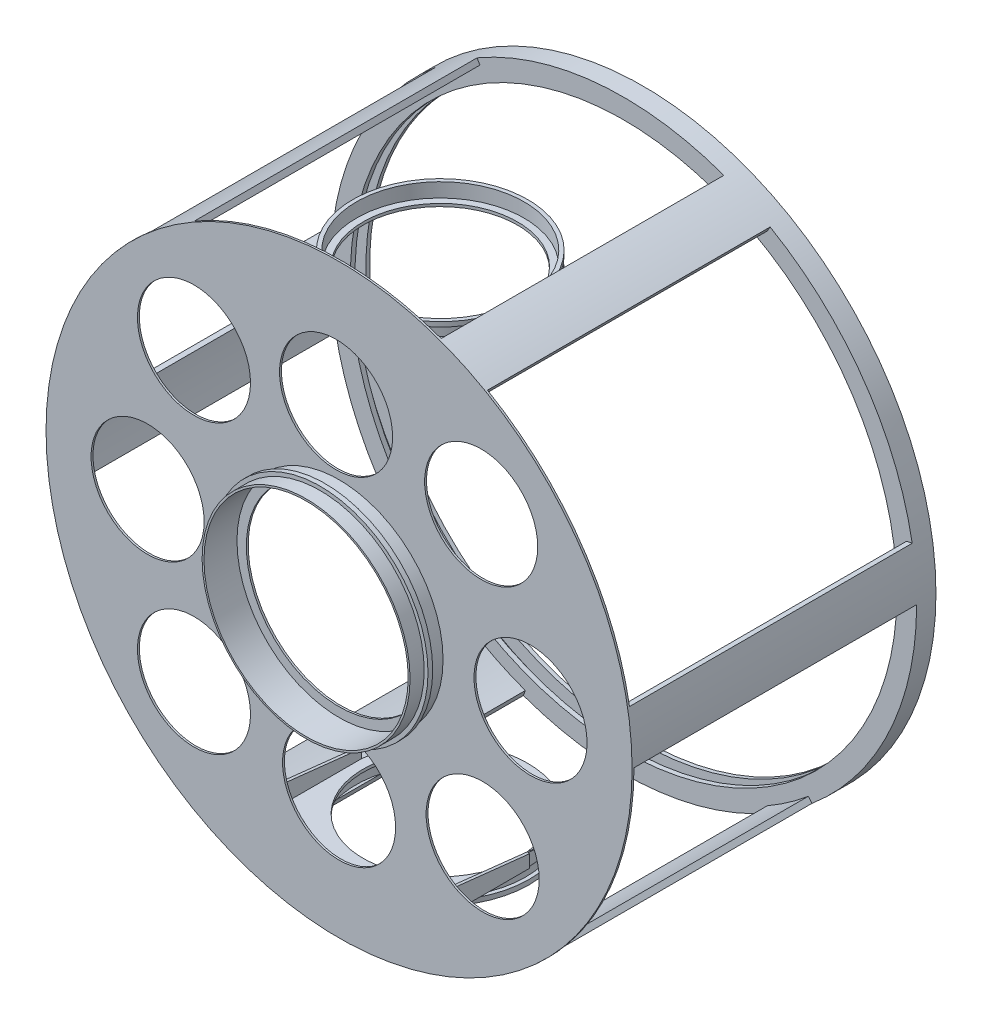
SolidWorks part; units mm, degrees
material "6063-T4"
ref_plane "Front Plane" through (0, 0, 0) normal (0, 0, 1) x (1, 0, 0)
ref_plane "Top Plane" through (0, 0, 0) normal (0, 1, 0) x (1, 0, 0)
ref_plane "Right Plane" through (0, 0, 0) normal (1, 0, 0) x (0, 0, -1)
sketch "Sketch1" plane through (0, 0, 0) normal (0, 0, 1) x (1, 0, 0)
  circle A0 centre (0, 0) radius 290.1
  circle A1 centre (0, 0) radius 311
extrude "Extrude1" add sketch "Sketch1" along normal blind 4
sketch "Sketch3" plane through (0, 0, 4) normal (0, 0, 1) x (1, 0, 0)
  circle A0 centre (0, 0) radius 311
  circle A1 centre (0, 0) radius 305
extrude "Extrude2" add sketch "Sketch3" along normal blind 11.5
sketch "Sketch4" plane through (0, 0, 15.5) normal (0, 0, 1) x (1, 0, 0)
  circle A0 centre (0, 0) radius 311
  circle A1 centre (0, 0) radius 290.1
extrude "Extrude3" add sketch "Sketch4" along normal blind 5
sketch "Sketch5" plane through (0, 0, 20.5) normal (0, 0, 1) x (1, 0, 0)
  line L0 (0, 0) -> (190.5, 0) construction
  line L1 (0, 0) -> (106.0987, 183.7684) construction
  line L2 (0, 0) -> (-108.3258, 187.6258) construction
  line L3 (0, 0) -> (-211.1375, 0) construction
  line L4 (0, 0) -> (-109.7214, -190.043) construction
  line L5 (0, 0) -> (117.9514, -204.2977) construction
  line L6 (0, 0) -> (268.0733, 47.2686) construction
  line L7 (0, 0) -> (77.8476, 213.8846) construction
  line L8 (0, 0) -> (-153.0298, 182.3738) construction
  line L9 (0, 0) -> (-259.4461, -45.7473) construction
  line L10 (0, 0) -> (-74.3455, -204.2625) construction
  line L11 (0, 0) -> (154.9569, -184.6704) construction
  line L12 (300.3664, 52.9627) -> (306.2752, 54.0046)
  line L13 (305, 0) -> (311, 0)
  line L14 (152.5, 264.1377) -> (155.5, 269.3339)
  line L15 (104.3161, 286.6062) -> (106.3683, 292.2444)
  line L16 (-152.5, 264.1377) -> (-155.5, 269.3339)
  line L17 (-196.0502, 233.6436) -> (-199.9069, 238.2398)
  line L18 (-305, 0) -> (-311, 0)
  line L19 (-300.3664, -52.9627) -> (-306.2752, -54.0046)
  line L20 (-152.5, -264.1377) -> (-155.5, -269.3339)
  line L21 (-104.3161, -286.6062) -> (-106.3683, -292.2444)
  line L22 (152.5, -264.1377) -> (155.5, -269.3339)
  line L23 (196.0502, -233.6436) -> (199.9069, -238.2398)
  circle A0 centre (0, 0) radius 311 construction
  circle A1 centre (0, 0) radius 305 construction
  arc A2 (300.3664, 52.9627) -> (305, 0) centre (0, 0) cw
  arc A3 (104.3161, 286.6062) -> (152.5, 264.1377) centre (0, 0) cw
  arc A4 (155.5, 269.3339) -> (106.3683, 292.2444) centre (0, 0) ccw
  arc A6 (-152.5, 264.1377) -> (-196.0502, 233.6436) centre (0, 0) ccw
  arc A7 (-155.5, 269.3339) -> (-199.9069, 238.2398) centre (0, 0) ccw
  arc A8 (-305, 0) -> (-300.3664, -52.9627) centre (0, 0) ccw
  arc A9 (-311, 0) -> (-306.2752, -54.0046) centre (0, 0) ccw
  arc A10 (-152.5, -264.1377) -> (-104.3161, -286.6062) centre (0, 0) ccw
  arc A11 (-155.5, -269.3339) -> (-106.3683, -292.2444) centre (0, 0) ccw
  arc A12 (152.5, -264.1377) -> (196.0502, -233.6436) centre (0, 0) ccw
  arc A13 (155.5, -269.3339) -> (199.9069, -238.2398) centre (0, 0) ccw
  arc A14 (311, 0) -> (306.2752, 54.0046) centre (0, 0) ccw
extrude "Extrude4" add sketch "Sketch5" along normal blind 300
sketch "Sketch6" plane through (0, 0, 320.5) normal (0, 0, 1) x (1, 0, 0)
  circle A0 centre (0, 0) radius 311
extrude "Extrude5" add sketch "Sketch6" along normal blind 2
sketch "Sketch7" plane through (0, 0, 322.5) normal (0, 0, 1) x (1, 0, 0)
  circle A0 centre (0, 0) radius 110.37
  circle A1 centre (0, 0) radius 108.37
extrude "Extrude6" add sketch "Sketch7" along normal blind 15
sketch "Sketch8" plane through (0, 0, 337.5) normal (0, 0, 1) x (1, 0, 0)
  circle A0 centre (0, 0) radius 108.37
  circle A1 centre (0, 0) radius 114.4
extrude "Extrude7" add sketch "Sketch8" along normal blind 5
sketch "Sketch9" plane through (0, 0, 342.5) normal (0, 0, 1) x (1, 0, 0)
  circle A0 centre (0, 0) radius 108.37
  circle A1 centre (0, 0) radius 110.37
extrude "Extrude8" add sketch "Sketch9" along normal blind 15
sketch "Sketch10" plane through (0, 0, 320.5) normal (0, 0, -1) x (-1, 0, 0)
  line L0 (0, 0) -> (0, 334.2218) construction
  line L1 (0, 0) -> (0, -343.8771) construction
  line L2 (0, 250) -> (502.8181, 250) construction
  line L3 (0, 250) -> (-514.35, 250) construction
  line L4 (0, -250) -> (542.182, -250) construction
  line L5 (0, -250) -> (-551.8374, -250) construction
  line L6 (0, 253) -> (404.821, 253) construction
  line L7 (0, 253) -> (-322.9253, 253) construction
  line L8 (0, -253) -> (377.1337, -253) construction
  line L9 (0, -253) -> (-458.931, -253) construction
  line L10 (94.96, 250) -> (94.96, 228)
  line L11 (94.96, 250) -> (94.96, 253)
  line L12 (94.96, 253) -> (0, 253)
  line L13 (0, 253) -> (-94.96, 253)
  line L14 (-94.96, 253) -> (-94.96, 250)
  line L15 (94.96, -250) -> (94.96, -228)
  line L16 (94.96, -250) -> (94.96, -253)
  line L17 (94.96, -253) -> (-94.96, -253)
  line L18 (-94.96, -253) -> (-94.96, -250)
  line L19 (94.96, 253) -> (94.96, 166.3555) construction
  line L20 (-94.96, 253) -> (-94.96, 171.8799) construction
  line L21 (94.96, -253) -> (94.96, -186.8569) construction
  line L22 (-94.96, -253) -> (-94.96, -186.8569) construction
  line L23 (94.96, -228) -> (-94.96, -228) construction
  line L24 (94.96, 228) -> (-94.96, 228) construction
  line L25 (94.96, 228) -> (91.96, 228)
  line L26 (91.96, 228) -> (91.96, 250)
  line L27 (91.96, 250) -> (-91.96, 250)
  line L28 (-91.96, 250) -> (-91.96, 228)
  line L29 (-91.96, 228) -> (-94.96, 228)
  line L30 (-94.96, 228) -> (-94.96, 250)
  line L31 (94.96, -228) -> (91.96, -228)
  line L32 (91.96, -228) -> (91.96, -250)
  line L33 (91.96, -250) -> (-91.96, -250)
  line L34 (-91.96, -250) -> (-91.96, -228)
  line L35 (-91.96, -228) -> (-94.96, -228)
  line L36 (-94.96, -228) -> (-94.96, -250)
  point P3 (0, 250)
  point P5 (0, -250)
  point P11 (0, 253)
  point P13 (0, -253)
  point P19 (94.96, 250)
  point P21 (-94.96, 250)
  point P22 (94.96, -250)
  point P23 (-94.96, -250)
  point P30 (94.96, 228)
  point P35 (-94.96, 228)
  point P36 (94.96, -228)
  point P38 (-94.96, -228)
  point P42 (91.96, -228)
  point P45 (-91.96, 228)
  point P46 (91.96, 228)
  point P47 (-91.96, -228)
  dimension "D1" = 250
  dimension "FROM_C" = 250
  dimension "D2" = 3
  dimension "D3" = 3
  dimension "D4" = 94.96
  dimension "RAD" = 94.96
  dimension "D5" = 94.96
  dimension "D6" = 94.96
  dimension "D7" = 25
  dimension "STRONG" = 25
  dimension "D8" = 25
  dimension "D9" = 25
  dimension "D10" = 3
  dimension "D11" = 3
  dimension "D12" = 3
extrude "Extrude9" add sketch "Sketch10" along normal blind 200
sketch "Sketch11" plane through (0, 253, 0) normal (0, 1, 0) x (1, 0, 0)
  line L0 (-94.96, -120.5) -> (94.96, -120.5) construction
  line L1 (0.3935, -99.9484) -> (0.3935, -349.6766) construction
  circle A0 centre (0.3935, -215.46) radius 90.96
  circle A1 centre (0.3935, -215.46) radius 88.96
  point P0 (0, -120.5)
  point P5 (0.3935, -215.46)
  dimension "D1" = 94.96
extrude "Extrude10" add sketch "Sketch11" along normal blind 10
sketch "Sketch13" plane through (0, 263, 0) normal (0, 1, 0) x (1, 0, 0)
  circle A0 centre (0.3935, -215.46) radius 88.96
  circle A1 centre (0.3935, -215.46) radius 92.96
extrude "Extrude11" add sketch "Sketch13" along normal blind 5
sketch "Sketch14" plane through (0, -253, 0) normal (0, -1, 0) x (1, 0, 0)
  line L0 (94.96, 120.5) -> (-94.96, 120.5) construction
  line L1 (0, 120.5) -> (0, 386.5869) construction
  circle A0 centre (0, 215.46) radius 88.96
  circle A1 centre (0, 215.46) radius 90.96
  point P0 (0, 120.5)
  point P5 (0, 215.46)
  dimension "D1" = 94.96
extrude "Extrude12" add sketch "Sketch14" along normal blind 10
sketch "Sketch15" plane through (0, -263, 0) normal (0, -1, 0) x (1, 0, 0)
  circle A0 centre (0, 215.46) radius 88.96
  circle A1 centre (0, 215.46) radius 94.96
extrude "Extrude13" add sketch "Sketch15" along normal blind 5
sketch "Sketch16" plane through (91.96, 0, 0) normal (-1, 0, 0) x (0, 0, 1)
  line L0 (120.5, 228) -> (320.5, 228) construction
  line L1 (120.5, 228) -> (320.5, 228)
  line L2 (320.5, 228) -> (120.5, 250)
  line L3 (120.5, 228) -> (120.5, 250)
  point P0 (220.5, 228)
  point P1 (120.5, 250)
  point P4 (120.5, 228)
  point P9 (320.5, 228)
extrude "Extrude14" cut sketch "Sketch16" against normal up to surface and the other way up to surface up to face at (94.96, 240.5, 220.5) other way up to face at (-94.96, 240.5, 220.5)
sketch "Sketch17" plane through (-91.96, 0, 0) normal (1, 0, 0) x (0, 0, -1)
  line L0 (-120.5, -228) -> (-320.5, -228) construction
  line L1 (-320.5, -228) -> (-120.5, -228)
  line L2 (-120.5, -228) -> (-120.5, -250)
  line L3 (-120.5, -250) -> (-320.5, -228)
  point P0 (-120.5, -250)
  point P1 (-220.5, -228)
  point P3 (-120.5, -228)
  point P6 (-320.5, -228)
extrude "Extrude15" cut sketch "Sketch17" against normal up to surface and the other way up to surface up to face at (-94.96, -240.5, 220.5) other way up to face at (94.96, -240.5, 220.5)
sketch "Sketch18" plane through (0, 253, 0) normal (0, 1, 0) x (1, 0, 0)
  line L1 (93.1735, -215.46) -> (94.96, -215.46)
  line L2 (94.96, -120.5) -> (94.96, -320.5) construction
  line L3 (94.96, -215.46) -> (94.96, -120.5)
  line L4 (94.96, -120.5) -> (-94.96, -120.5)
  line L5 (-94.96, -120.5) -> (-94.96, -215.46)
  line L6 (-94.96, -120.5) -> (-94.96, -320.5) construction
  line L7 (-94.96, -215.46) -> (-92.3865, -215.46)
  circle A0 centre (69.85, -304.8) radius 11.1125
  circle A1 centre (-69.85, -304.8) radius 11.1125
  circle A2 centre (0.3935, -215.46) radius 92.78 construction
  arc A3 (93.1735, -215.46) -> (-92.3865, -215.46) centre (0.3935, -215.46) ccw
  circle A4 centre (0.3935, -215.46) radius 82
  point P9 (94.96, -120.5)
  point P12 (-94.96, -120.5)
extrude "Extrude16" cut sketch "Sketch18" against normal blind 25
sketch "Sketch19" plane through (0, -253, 0) normal (0, -1, 0) x (1, 0, 0)
  line L1 (93.1735, 215.46) -> (94.96, 215.46)
  line L2 (94.96, 215.46) -> (94.96, 120.5)
  line L3 (94.96, 120.5) -> (-94.96, 120.5)
  line L4 (-94.96, 120.5) -> (-94.96, 215.46)
  line L5 (-94.96, 215.46) -> (-92.3865, 215.46)
  circle A0 centre (69.85, 304.8) radius 11.1125
  circle A1 centre (-69.85, 304.8) radius 11.1125
  circle A2 centre (0.3935, 215.46) radius 92.78 construction
  arc A3 (93.1735, 215.46) -> (-92.3865, 215.46) centre (0.3935, 215.46) cw
  circle A4 centre (0, 215.46) radius 94.96 construction
  circle A5 centre (0.3935, 215.46) radius 82
  point P0 (69.85, 304.8)
  point P1 (-69.85, 304.8)
  point P8 (0.3935, 215.46)
extrude "Extrude18" cut sketch "Sketch19" against normal blind 25
sketch "Sketch20" plane through (0, 0, 322.5) normal (0, 0, 1) x (1, 0, 0)
  circle A0 centre (0, 0) radius 98.425
  circle A1 centre (203.2, 0) radius 60
  circle A2 centre (150.8125, 153.9875) radius 60
  circle A3 centre (-3.175, 177.8) radius 60
  circle A4 centre (-153.9875, 152.4) radius 60
  circle A5 centre (-203.2, 0) radius 60
  circle A6 centre (-153.9875, -152.4) radius 60
  circle A7 centre (0, -179.3875) radius 60
  circle A8 centre (152.4, -150.8125) radius 60
  point P3 (-153.9875, 152.4)
  point P4 (150.8125, 153.9875)
  point P5 (152.4, -150.8125)
  point P6 (-153.9875, -152.4)
  point P7 (203.2, 0)
  point P8 (-203.2, 0)
  point P9 (-3.175, 177.8)
  point P10 (0, -179.3875)
extrude "Extrude19" cut sketch "Sketch20" against normal up to surface (2 mm away) up to face at (0, 239.75, 320.5)
equation "\"D1@Sketch10\" = \"FROM_C\""
equation "\"D4@Sketch10\" = \"RAD\""
equation "\"D5@Sketch10\" = \"RAD\""
equation "\"D6@Sketch10\" = \"RAD\""
equation "\"D7@Sketch10\" = \"STRONG\""
equation "\"D8@Sketch10\" = \"STRONG\""
equation "\"D9@Sketch10\" = \"STRONG\""
